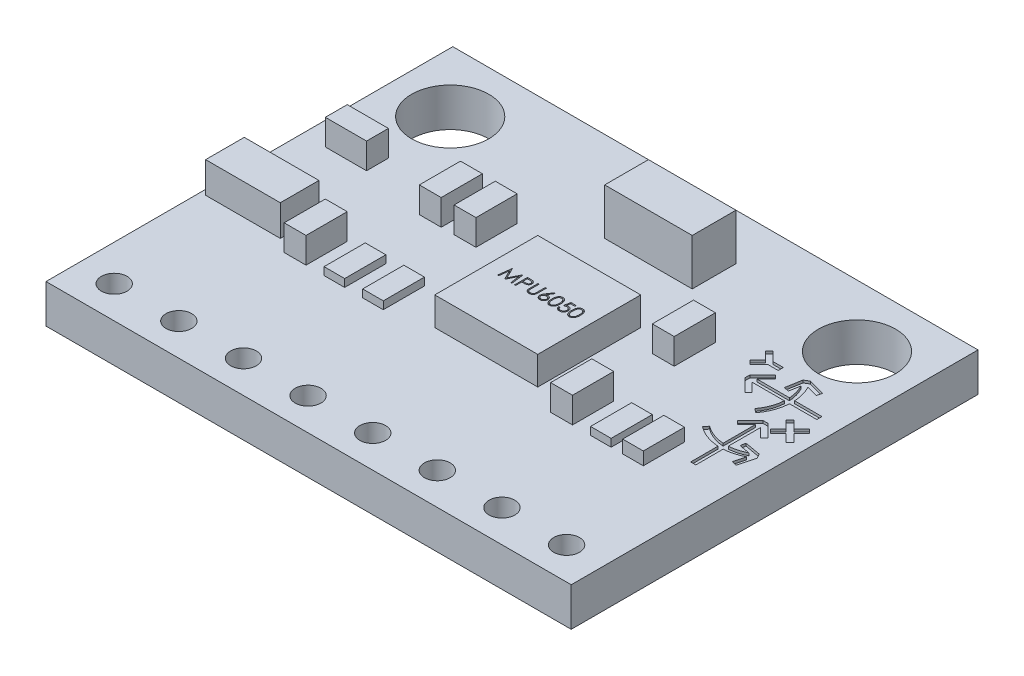
SolidWorks part; units mm, degrees
ref_plane "Front Plane" through (0, 0, 0) normal (0, 0, 1) x (1, 0, 0)
ref_plane "Top Plane" through (0, 0, 0) normal (0, 1, 0) x (1, 0, 0)
ref_plane "Right Plane" through (0, 0, 0) normal (1, 0, 0) x (0, 0, -1)
sketch "Sketch1" plane through (0, 0, 0) normal (0, 1, 0) x (1, 0, 0)
  line L1 (10.2, -7.9) -> (-10.2, -7.9)
  line L2 (10.2, -7.9) -> (10.2, 7.9)
  line L3 (10.2, 7.9) -> (-10.2, 7.9)
  line L4 (-10.2, -7.9) -> (-10.2, 7.9)
  line L5 (10.2, -7.9) -> (-10.2, 7.9) construction
  line L6 (10.2, 7.9) -> (-10.2, -7.9) construction
  point P0 (0, 0)
  dimension "D1" = 20.4
  dimension "D2" = 15.8
extrude "Boss-Extrude1" add sketch "Sketch1" along normal blind 1.5
sketch "Sketch2" plane through (0, 1.5, 0) normal (0, 1, 0) x (1, 0, 0)
  line L0 (0, 0) -> (0, 7.9) construction
  line L1 (10.2, 7.9) -> (-10.2, 7.9) construction
  line L2 (-10.2, 7.9) -> (-10.2, -7.9) construction
  circle A0 centre (-7.9, 5.5) radius 1.5
  circle A1 centre (7.9, 5.5) radius 1.5
  dimension "D1" = 3
  dimension "D2" = 2.3
  dimension "D3" = 2.4
extrude "Cut-Extrude1" cut sketch "Sketch2" against normal up to next
sketch "Sketch3" plane through (0, 1.5, 0) normal (0, 1, 0) x (1, 0, 0)
  line L0 (-9.3, -7.15) -> (9.3, -7.15) construction
  line L1 (-10.2, -7.9) -> (10.2, -7.9) construction
  line L2 (9.3, -3.5805) -> (9.3, -7.15) construction
  line L3 (10.2, -7.9) -> (10.2, 7.9) construction
  line L4 (0, 0) -> (0, 7.9) construction
  line L5 (10.2, 7.9) -> (-10.2, 7.9) construction
  line L6 (-9.3, -3.5805) -> (-9.3, -7.15) construction
  circle A0 centre (-8.8, -6.65) radius 0.5
  circle A1 centre (-6.29, -6.65) radius 0.5
  circle A2 centre (-3.78, -6.65) radius 0.5
  circle A3 centre (-1.27, -6.65) radius 0.5
  circle A4 centre (1.24, -6.65) radius 0.5
  circle A5 centre (3.75, -6.65) radius 0.5
  circle A6 centre (6.26, -6.65) radius 0.5
  circle A7 centre (8.77, -6.65) radius 0.5
  dimension "D3" = 1
  dimension "D1" = 0.75
  dimension "D2" = 0.9
  dimension "D4" = 8
extrude "Cut-Extrude2" cut sketch "Sketch3" against normal up to next
sketch "Sketch4" plane through (0, 1.5, 0) normal (0, 1, 0) x (1, 0, 0)
  line L0 (10.2, 7.9) -> (-10.2, 7.9) construction
  line L1 (-0.8, 6.1) -> (2.6, 6.1)
  line L2 (-0.8, 6.1) -> (-0.8, 4.4)
  line L3 (-0.8, 4.4) -> (2.6, 4.4)
  line L4 (2.6, 6.1) -> (2.6, 4.4)
  line L5 (-0.8, 6.1) -> (2.6, 4.4) construction
  line L6 (-0.8, 4.4) -> (2.6, 6.1) construction
  line L7 (10.2, -7.9) -> (10.2, 7.9) construction
  point P0 (0.9, 5.25)
  dimension "D1" = 3.4
  dimension "D2" = 1.7
  dimension "D3" = 1.8
  dimension "D4" = 7.6
extrude "Boss-Extrude2" add sketch "Sketch4" along normal blind 1.8
sketch "Sketch5" plane through (0, 1.5, 0) normal (0, 1, 0) x (1, 0, 0)
  line L0 (10.2, -7.9) -> (10.2, 7.9) construction
  line L1 (-1.1, 2.1) -> (2.9, 2.1)
  line L2 (-1.1, 2.1) -> (-1.1, -1.9)
  line L3 (-1.1, -1.9) -> (2.9, -1.9)
  line L4 (2.9, 2.1) -> (2.9, -1.9)
  line L5 (-1.1, 2.1) -> (2.9, -1.9) construction
  line L6 (-1.1, -1.9) -> (2.9, 2.1) construction
  line L7 (-10.2, -7.9) -> (10.2, -7.9) construction
  point P0 (0.9, 0.1)
  dimension "D1" = 7.3
  dimension "D2" = 6
  dimension "D3" = 4
  dimension "D4" = 4
extrude "Boss-Extrude3" add sketch "Sketch5" along normal blind 1.1
sketch "Sketch11" plane through (0, 2.6, 0) normal (0, 1, 0) x (1, 0, 0)
  text T0 "MPU6050" font "Century Gothic" height 0.5
extrude "Cut-Extrude3" cut sketch "Sketch11" against normal blind 0.1
sketch "Sketch6" plane through (0, 1.5, 0) normal (0, 1, 0) x (1, 0, 0)
  line L0 (-10.2, 7.9) -> (-10.2, -7.9) construction
  line L1 (-10, -0.4) -> (-7.1, -0.4)
  line L2 (-10, -0.4) -> (-10, -1.9)
  line L3 (-10, -1.9) -> (-7.1, -1.9)
  line L4 (-7.1, -0.4) -> (-7.1, -1.9)
  line L5 (-10, -0.4) -> (-7.1, -1.9) construction
  line L6 (-10, -1.9) -> (-7.1, -0.4) construction
  line L7 (-10.2, -7.9) -> (10.2, -7.9) construction
  point P0 (-8.55, -1.15)
  dimension "D1" = 0.2
  dimension "D2" = 6
  dimension "D3" = 2.9
  dimension "D4" = 1.5
extrude "Boss-Extrude4" add sketch "Sketch6" along normal blind 1.2
sketch "Sketch7" plane through (0, 1.5, 0) normal (0, 1, 0) x (1, 0, 0)
  line L0 (-10.2, -7.9) -> (10.2, -7.9) construction
  line L1 (-5.7, -2.3) -> (-6.55, -2.3)
  line L2 (-5.7, -2.3) -> (-5.7, -0.7)
  line L3 (-5.7, -0.7) -> (-6.55, -0.7)
  line L4 (-6.55, -2.3) -> (-6.55, -0.7)
  line L5 (-5.7, -2.3) -> (-6.55, -0.7) construction
  line L6 (-5.7, -0.7) -> (-6.55, -2.3) construction
  line L7 (-10.2, 7.9) -> (-10.2, -7.9) construction
  line L8 (10.2, 7.9) -> (-10.2, 7.9) construction
  line L9 (-9.3, 2.9) -> (-7.7, 2.9)
  line L10 (-9.3, 2.9) -> (-9.3, 2.05)
  line L11 (-9.3, 2.05) -> (-7.7, 2.05)
  line L12 (-7.7, 2.9) -> (-7.7, 2.05)
  line L13 (-9.3, 2.9) -> (-7.7, 2.05) construction
  line L14 (-9.3, 2.05) -> (-7.7, 2.9) construction
  line L15 (10.2, -7.9) -> (10.2, 7.9) construction
  line L16 (-5.2, 3.2) -> (-4.35, 3.2)
  line L17 (-5.2, 3.2) -> (-5.2, 1.6)
  line L18 (-5.2, 1.6) -> (-4.35, 1.6)
  line L19 (-4.35, 3.2) -> (-4.35, 1.6)
  line L20 (-3.85, 3.2) -> (-3, 3.2)
  line L21 (-3.85, 3.2) -> (-3.85, 1.6)
  line L22 (-3.85, 1.6) -> (-3, 1.6)
  line L23 (-3, 3.2) -> (-3, 1.6)
  line L24 (4, 3.05) -> (4.85, 3.05)
  line L25 (4, 3.05) -> (4, 1.45)
  line L26 (4, 1.45) -> (4.85, 1.45)
  line L27 (4.85, 3.05) -> (4.85, 1.45)
  line L29 (4, -0.9) -> (4.85, -0.9)
  line L30 (4, -0.9) -> (4, -2.5)
  line L31 (4, -2.5) -> (4.85, -2.5)
  line L32 (4.85, -0.9) -> (4.85, -2.5)
  point P0 (-6.125, -1.5)
  point P9 (-8.5, 2.475)
  dimension "D1" = 0.85
  dimension "D2" = 1.6
  dimension "D3" = 5.6
  dimension "D4" = 4.5
  dimension "D5" = 5
  dimension "D6" = 0.9
  dimension "D7" = 4.7
  dimension "D8" = 0.5
  dimension "D9" = 5
  dimension "D10" = 4.85
  dimension "D11" = 6.2
  dimension "D12" = 5.4
extrude "Boss-Extrude5" add sketch "Sketch7" along normal blind 1
sketch "Sketch8" plane through (0, 1.5, 0) normal (0, 1, 0) x (1, 0, 0)
  line L0 (-5.7, -2.3) -> (-5.7, -0.7) construction
  line L1 (-4.2, -2.3) -> (-5, -2.3)
  line L2 (-4.2, -2.3) -> (-4.2, -0.7)
  line L3 (-4.2, -0.7) -> (-5, -0.7)
  line L4 (-5, -2.3) -> (-5, -0.7)
  line L5 (-4.2, -2.3) -> (-5, -0.7) construction
  line L6 (-4.2, -0.7) -> (-5, -2.3) construction
  line L7 (-2.7, -2.3) -> (-3.5, -2.3)
  line L8 (-2.7, -2.3) -> (-2.7, -0.7)
  line L9 (-2.7, -0.7) -> (-3.5, -0.7)
  line L10 (-3.5, -2.3) -> (-3.5, -0.7)
  line L11 (-2.7, -2.3) -> (-3.5, -0.7) construction
  line L12 (-2.7, -0.7) -> (-3.5, -2.3) construction
  line L13 (-6.55, -2.3) -> (-5.7, -2.3) construction
  line L14 (4.85, -0.9) -> (4, -0.9) construction
  line L15 (5.55, -0.9) -> (6.35, -0.9)
  line L16 (5.55, -0.9) -> (5.55, -2.5)
  line L17 (5.55, -2.5) -> (6.35, -2.5)
  line L18 (6.35, -0.9) -> (6.35, -2.5)
  line L19 (4.85, -2.5) -> (4.85, -0.9) construction
  point P0 (-4.6, -1.5)
  point P5 (-3.1, -1.5)
  dimension "D1" = 0.8
  dimension "D2" = 1.6
  dimension "D3" = 0.7
  dimension "D5" = 0.7
  dimension "D6" = 0.7
extrude "Boss-Extrude6" add sketch "Sketch8" along normal blind 0.3
sketch "Sketch10" plane through (0, 1.5, 0) normal (0, 1, 0) x (1, 0, 0)
  line L0 (10.2, -7.9) -> (10.2, 7.9) construction
  line L1 (6.8, -0.9) -> (7.6, -0.9)
  line L2 (6.8, -0.9) -> (6.8, -2.5)
  line L3 (6.8, -2.5) -> (7.6, -2.5)
  line L4 (7.6, -0.9) -> (7.6, -2.5)
  line L6 (5.55, -2.5) -> (6.35, -2.5) construction
  dimension "D1" = 0.8
  dimension "D2" = 1.6
  dimension "D3" = 2.6
extrude "Boss-Extrude8" add sketch "Sketch10" along normal blind 0.5
sketch "Sketch12" plane through (0, 1.5, 0) normal (0, 1, 0) x (1, 0, 0)
  line L0 (9.7321, 1.2176) -> (9.4321, 1.5176)
  line L1 (9.4321, 1.5176) -> (9.7321, 1.8176)
  line L2 (9.7321, 1.8176) -> (9.5821, 1.9676)
  line L3 (9.5821, 1.9676) -> (9.2821, 1.6676)
  line L4 (9.2821, 1.6676) -> (8.9821, 1.9676)
  line L5 (8.9821, 1.9676) -> (8.8321, 1.8176)
  line L6 (8.8321, 1.8176) -> (9.1321, 1.5176)
  line L7 (9.1321, 1.5176) -> (8.8321, 1.2176)
  line L8 (8.8321, 1.2176) -> (8.9821, 1.0676)
  line L9 (8.9821, 1.0676) -> (9.2821, 1.3676)
  line L10 (9.2821, 1.3676) -> (9.5821, 1.0676)
  line L11 (9.5821, 1.0676) -> (9.7321, 1.2176)
  line L12 (7.554, 0.1244) -> (7.4326, -0.0349)
  line L13 (8.3888, -0.3889) -> (8.3888, -1.449)
  line L14 (8.3888, -1.449) -> (8.5888, -1.449)
  line L15 (8.5888, -1.449) -> (8.5888, -0.3889)
  line L16 (9.3051, -0.189) -> (9.1873, -0.6284)
  line L17 (9.1873, -0.6284) -> (9.3805, -0.6802)
  line L18 (9.3805, -0.6802) -> (9.5554, -0.0276)
  line L19 (9.5554, -0.0276) -> (9.4494, 0.1483)
  line L20 (9.4494, 0.1483) -> (8.8322, 0.2571)
  line L21 (8.8322, 0.2571) -> (8.7974, 0.0601)
  line L22 (8.7974, 0.0601) -> (9.2102, -0.0126)
  line L23 (8.5888, -0.1883) -> (8.5888, 1.067)
  line L24 (8.5888, 1.067) -> (8.9413, 0.7145)
  line L25 (8.9413, 0.7145) -> (9.0827, 0.8559)
  line L26 (9.0827, 0.8559) -> (8.5876, 1.351)
  line L27 (8.5876, 1.351) -> (8.3909, 1.351)
  line L28 (8.3909, 1.351) -> (7.8964, 0.8565)
  line L29 (7.8964, 0.8565) -> (8.0378, 0.7151)
  line L30 (8.0378, 0.7151) -> (8.3888, 1.066)
  line L31 (8.3888, 1.066) -> (8.3888, -0.1882)
  line L32 (6.1121, 3.7273) -> (6.4121, 3.4273)
  line L33 (6.4121, 3.4273) -> (6.1121, 3.1273)
  line L34 (6.1121, 3.1273) -> (6.2621, 2.9773)
  line L35 (6.2621, 2.9773) -> (6.6121, 3.3273)
  line L36 (6.6121, 3.3273) -> (7.0121, 3.3273)
  line L37 (7.0121, 3.3273) -> (7.0121, 3.5273)
  line L38 (7.0121, 3.5273) -> (6.6121, 3.5273)
  line L39 (6.6121, 3.5273) -> (6.2621, 3.8773)
  line L40 (6.2621, 3.8773) -> (6.1121, 3.7273)
  line L41 (6.8971, 2.4273) -> (8.1514, 2.4273)
  line L42 (7.8388, 1.5925) -> (7.9981, 1.4711)
  line L43 (8.3521, 2.4273) -> (9.4121, 2.4273)
  line L44 (9.4121, 2.4273) -> (9.4121, 2.6273)
  line L45 (9.4121, 2.6273) -> (8.3521, 2.6273)
  line L46 (8.1522, 3.3436) -> (8.5916, 3.2259)
  line L47 (8.5916, 3.2259) -> (8.6434, 3.419)
  line L48 (8.6434, 3.419) -> (7.9908, 3.5939)
  line L49 (7.9908, 3.5939) -> (7.8149, 3.488)
  line L50 (7.8149, 3.488) -> (7.7061, 2.8707)
  line L51 (7.7061, 2.8707) -> (7.903, 2.8359)
  line L52 (7.903, 2.8359) -> (7.9758, 3.2487)
  line L53 (8.1514, 2.6273) -> (6.8962, 2.6273)
  line L54 (6.8962, 2.6273) -> (7.2487, 2.9798)
  line L55 (7.2487, 2.9798) -> (7.1073, 3.1213)
  line L56 (7.1073, 3.1213) -> (6.6121, 2.6261)
  line L57 (6.6121, 2.6261) -> (6.6121, 2.4294)
  line L58 (6.6121, 2.4294) -> (7.1066, 1.9349)
  line L59 (7.1066, 1.9349) -> (7.2481, 2.0763)
  line L60 (7.2481, 2.0763) -> (6.8971, 2.4273)
  arc A0 (7.554, 0.1244) -> (8.3888, -0.1882) centre (8.4893, 1.351) ccw
  arc A1 (7.4326, -0.0349) -> (8.3888, -0.3889) centre (8.4893, 1.351) ccw
  arc A2 (8.5888, -0.3889) -> (9.3051, -0.189) centre (8.4893, 1.351) ccw
  arc A3 (8.5888, -0.1883) -> (9.2102, -0.0126) centre (8.4893, 1.351) ccw
  arc A4 (7.8388, 1.5925) -> (8.1514, 2.4273) centre (6.6121, 2.5278) ccw
  arc A5 (7.9981, 1.4711) -> (8.3521, 2.4273) centre (6.6121, 2.5278) ccw
  arc A6 (8.3521, 2.6273) -> (8.1522, 3.3436) centre (6.6121, 2.5278) ccw
  arc A7 (8.1514, 2.6273) -> (7.9758, 3.2487) centre (6.6121, 2.5278) ccw
extrude "Cut-Extrude4" cut sketch "Sketch12" against normal blind 0.1
sketch "Sketch13" plane through (0, 0, 0) normal (0, -1, 0) x (1, 0, 0)
  line L0 (-10.2, 7.9) -> (10.2, -7.9) construction
  circle A0 centre (0, 0) radius 1
  dimension "D1" = 2
extrude "Boss-Extrude9" add sketch "Sketch13" along normal blind 1
